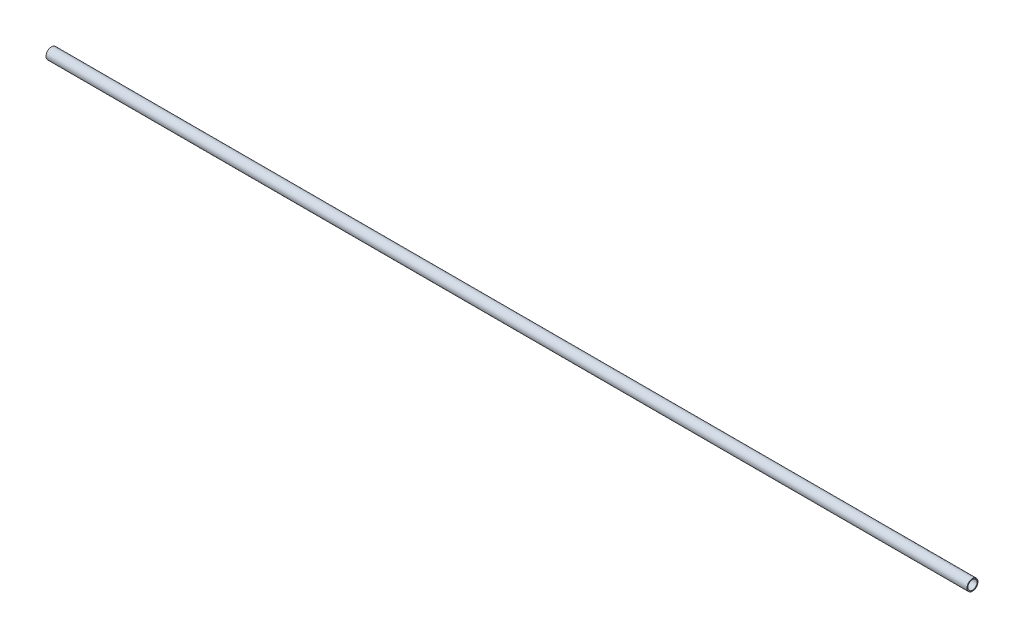
SolidWorks part; units mm, degrees
ref_plane "Front Plane" through (0, 0, 0) normal (0, 0, 1) x (1, 0, 0)
ref_plane "Top Plane" through (0, 0, 0) normal (0, 1, 0) x (1, 0, 0)
ref_plane "Right Plane" through (0, 0, 0) normal (1, 0, 0) x (0, 0, -1)
sketch "Sketch1" plane through (0, 0, 0) normal (1, 0, 0) x (0, 0, -1)
  circle A0 centre (0, 0) radius 2.5
  circle A1 centre (0, 0) radius 3
  dimension "D1" = 5
  dimension "D2" = 6
extrude "spar_extrude" add sketch "Sketch1" along normal blind 500
